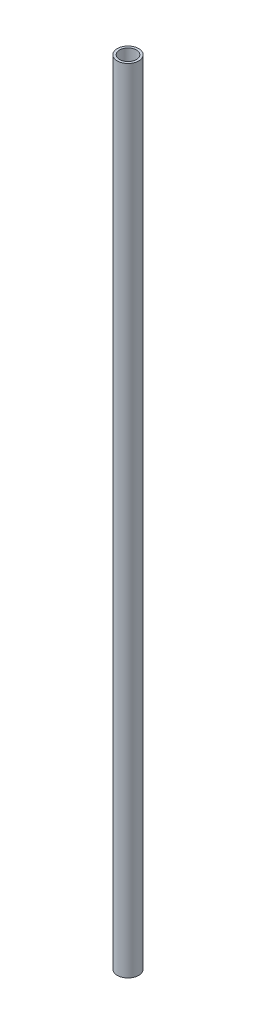
SolidWorks part; units mm, degrees
material "Thornel VCB-20 Carbon Cloth"
ref_plane "Front Plane" through (0, 0, 0) normal (0, 0, 1) x (1, 0, 0)
ref_plane "Top Plane" through (0, 0, 0) normal (0, 1, 0) x (1, 0, 0)
ref_plane "Right Plane" through (0, 0, 0) normal (1, 0, 0) x (0, 0, -1)
sketch "Sketch1" plane through (0, 0, 0) normal (0, 1, 0) x (1, 0, 0)
  circle A0 centre (0, 0) radius 4.064
  circle A1 centre (0, 0) radius 3.175
  dimension "D1" = 8.128
  dimension "D2" = 6.35
extrude "Boss-Extrude1" add sketch "Sketch1" along normal blind 300
